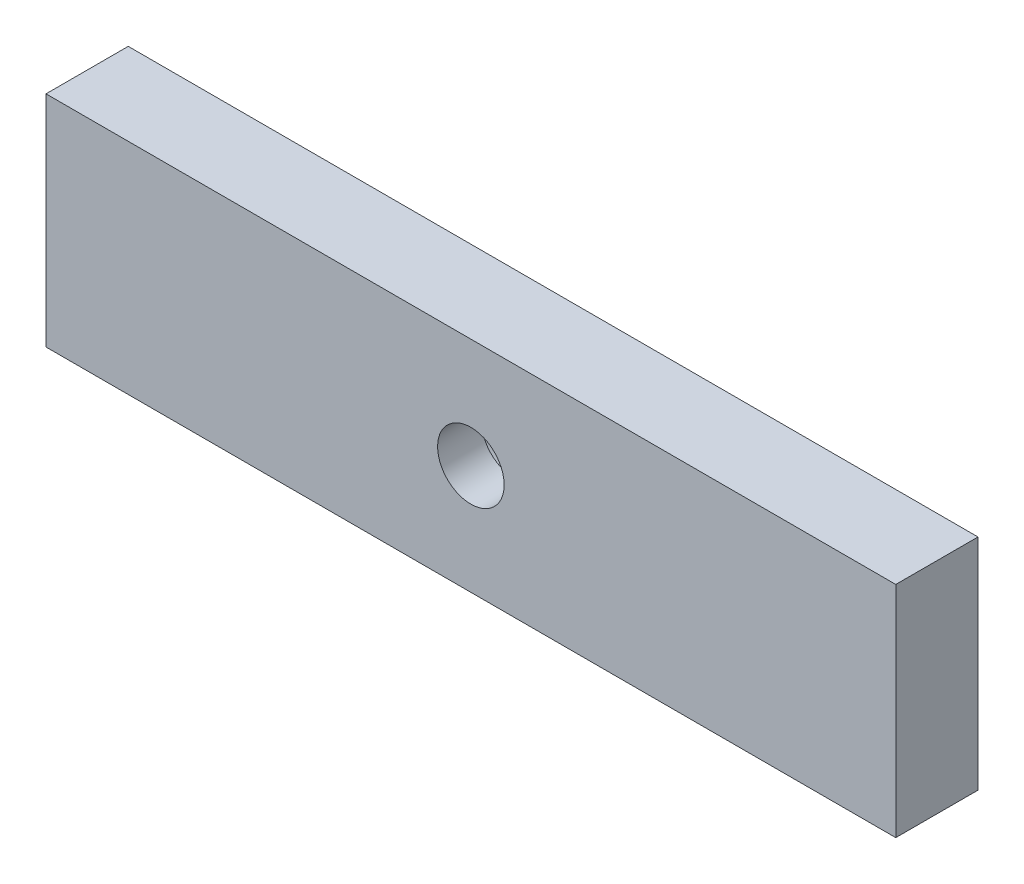
SolidWorks part; units mm, degrees
ref_plane "Front Plane" through (0, 0, 0) normal (0, 0, 1) x (1, 0, 0)
ref_plane "Top Plane" through (0, 0, 0) normal (0, 1, 0) x (1, 0, 0)
ref_plane "Right Plane" through (0, 0, 0) normal (1, 0, 0) x (0, 0, -1)
sketch "Sketch1" plane through (0, 0, 0) normal (0, 0, 1) x (1, 0, 0)
  line L1 (-77.5, 20) -> (77.5, 20)
  line L2 (-77.5, 20) -> (-77.5, -20)
  line L3 (-77.5, -20) -> (77.5, -20)
  line L4 (77.5, 20) -> (77.5, -20)
  line L5 (-77.5, 20) -> (77.5, -20) construction
  line L6 (-77.5, -20) -> (77.5, 20) construction
  point P0 (0, 0)
  dimension "D1" = 155
  dimension "D2" = 40
extrude "Boss-Extrude1" add sketch "Sketch1" along normal blind 15
sketch "Sketch2" plane through (0, 0, 0) normal (0, 0, -1) x (-1, 0, 0)
  circle A0 centre (0, 0) radius 11
extrude "Cut-Extrude1" cut sketch "Sketch2" against normal blind 7
sketch "Sketch3" plane through (0, 0, 0) normal (0, 0, -1) x (-1, 0, 0)
  circle A0 centre (0, 0) radius 6.0708
  point P3 (0, 0)
extrude "Cut-Extrude2" cut sketch "Sketch3" against normal up to vertex
